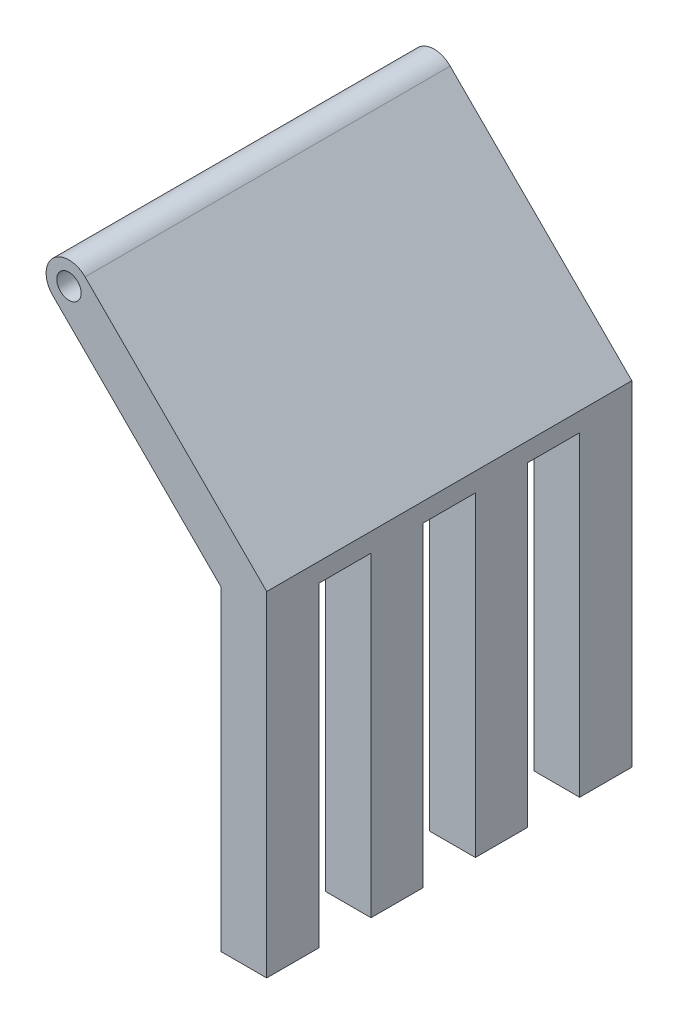
SolidWorks part; units mm, degrees
ref_plane "Front Plane" through (0, 0, 0) normal (0, 0, 1) x (1, 0, 0)
ref_plane "Top Plane" through (0, 0, 0) normal (0, 1, 0) x (1, 0, 0)
ref_plane "Right Plane" through (0, 0, 0) normal (1, 0, 0) x (0, 0, -1)
sketch "Sketch1" plane through (0, 0, 0) normal (0, 0, 1) x (1, 0, 0)
  line L0 (0, 0) -> (0, 51.8934)
  line L1 (0, 51.8934) -> (-27.6517, 79.545)
  line L2 (0, 0) -> (7.5, 0)
  line L3 (7.5, 0) -> (7.5, 55)
  line L4 (7.5, 55) -> (-22.3483, 84.8483)
  line L8 (-27.6517, 79.545) -> (-22.3483, 84.8483) construction
  circle A0 centre (-25, 82.1967) radius 2
  arc A1 (-27.6517, 79.545) -> (-22.3483, 84.8483) centre (-25, 82.1967) cw
  dimension "D6" = 4
  dimension "D1" = 7.5
  dimension "D3" = 225
  dimension "D4" = 55
  dimension "D5" = 25
extrude "Boss-Extrude1" add sketch "Sketch1" along normal blind 60
sketch "Sketch2" plane through (0, 0, 0) normal (-1, 0, 0) x (0, 0, 1)
  line L0 (60, 51.8934) -> (0, 51.8934) construction
  line L6 (25.7143, 51.8934) -> (34.2857, 51.8934)
  line L10 (25.7143, 51.8934) -> (25.7143, 0)
  line L13 (25.7143, 0) -> (34.2857, 0)
  line L14 (34.2857, 51.8934) -> (34.2857, 0)
  line L15 (60, 0) -> (0, 0) construction
  line L17 (42.8571, 51.8934) -> (51.4286, 51.8934)
  line L18 (42.8571, 51.8934) -> (42.8571, 0)
  line L19 (42.8571, 0) -> (51.4286, 0)
  line L20 (51.4286, 51.8934) -> (51.4286, 0)
  line L21 (0, 0) -> (8.5714, 0) construction
  line L22 (8.5714, 51.8934) -> (17.1429, 51.8934)
  line L23 (8.5714, 51.8934) -> (8.5714, 0)
  line L24 (8.5714, 0) -> (17.1429, 0)
  line L25 (17.1429, 51.8934) -> (17.1429, 0)
  line L26 (17.1429, 0) -> (25.7143, 0) construction
  line L27 (34.2857, 0) -> (42.8571, 0) construction
  line L28 (51.4286, 0) -> (60, 0) construction
extrude "Cut-Extrude1" cut sketch "Sketch2" against normal through all
